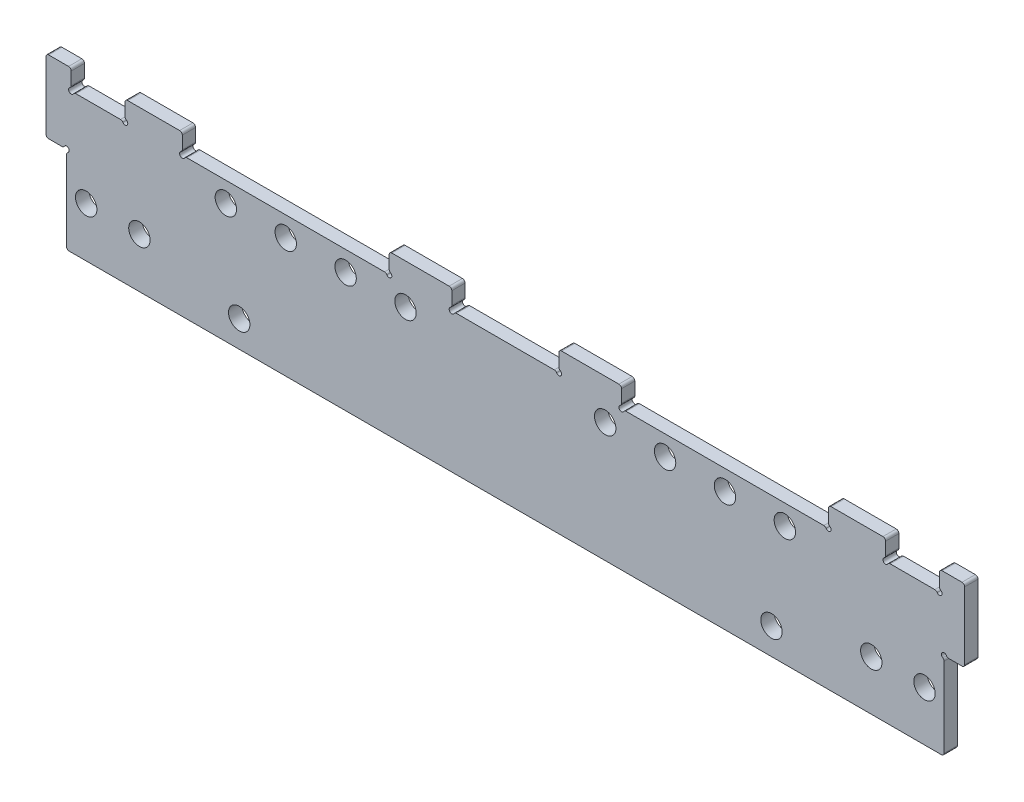
SolidWorks part; units mm, degrees
material "AISI Type A2 Tool Steel"
ref_plane "Front Plane" through (0, 0, 0) normal (0, 0, 1) x (1, 0, 0)
ref_plane "Top Plane" through (0, 0, 0) normal (0, 1, 0) x (1, 0, 0)
ref_plane "Right Plane" through (0, 0, 0) normal (1, 0, 0) x (0, 0, -1)
sketch "Top Layout" plane through (0, 0, 0) normal (0, 1, 0) x (1, 0, 0)
  line L0 (-114.046, -123.825) -> (-104.775, -123.825) construction
  line L1 (-104.775, -142.875) -> (-101.6, -142.875)
  line L2 (-104.775, -142.875) -> (-104.775, -104.775)
  line L3 (-104.775, -104.775) -> (-101.6, -104.775)
  line L4 (-101.6, -142.875) -> (-101.6, -104.775)
  line L5 (-104.775, -142.875) -> (-101.6, -104.775) construction
  line L6 (-104.775, -104.775) -> (-101.6, -142.875) construction
  line L7 (-19.05, -105.8164) -> (-101.6, -105.8164)
  line L8 (-19.05, -105.8164) -> (-19.05, -141.8336)
  line L9 (-19.05, -141.8336) -> (-101.6, -141.8336)
  line L10 (-101.6, -105.8164) -> (-101.6, -141.8336)
  line L11 (-19.05, -105.8164) -> (-101.6, -141.8336) construction
  line L12 (-19.05, -141.8336) -> (-101.6, -105.8164) construction
  line L13 (-133.096, -85.725) -> (-114.046, -85.725)
  line L14 (-133.096, -85.725) -> (-133.096, -161.925)
  line L15 (-133.096, -161.925) -> (-114.046, -161.925)
  line L16 (-114.046, -85.725) -> (-114.046, -161.925)
  line L17 (-133.096, -85.725) -> (-114.046, -161.925) construction
  line L18 (-133.096, -161.925) -> (-114.046, -85.725) construction
  line L19 (-104.775, -123.825) -> (0, -123.825) construction
  line L20 (0, -123.825) -> (0, 0) construction
  line L21 (-52.3528, -40.1717) -> (0, 0) construction
  line L22 (-70.6449, -16.3328) -> (-18.2922, 23.8388)
  line L23 (-34.0606, -64.0105) -> (18.2922, -23.8388)
  line L24 (-30.9251, 40.3023) -> (-122.2248, -29.7544)
  line L25 (-153.9748, -53.975) -> (-153.9748, -123.825)
  line L26 (-109.5248, -162.052) -> (109.5248, -162.052)
  line L27 (0, -162.052) -> (0, -123.825) construction
  line L28 (-109.5248, -162.052) -> (-109.5248, -20.0093) construction
  line L29 (-104.775, -142.875) -> (-104.775, -152.527)
  line L30 (-104.775, -152.527) -> (104.775, -152.527)
  line L31 (104.775, -104.775) -> (101.6, -104.775)
  line L32 (-144.4498, -73.025) -> (-109.5248, -73.025)
  line L33 (-144.4498, -73.025) -> (-144.4498, -123.825)
  line L34 (-144.4498, -123.825) -> (-109.5248, -123.825) construction
  line L35 (-109.5248, -73.025) -> (-109.5248, -162.052)
  line L36 (-144.4498, -73.025) -> (-109.5248, -123.825) construction
  line L37 (-144.4498, -123.825) -> (-109.5248, -73.025) construction
  line L38 (101.6, -142.875) -> (101.6, -104.775)
  line L39 (104.775, -142.875) -> (101.6, -142.875)
  line L40 (104.775, -142.875) -> (104.775, -104.775)
  line L41 (104.775, -142.875) -> (104.775, -152.527)
  line L42 (109.5248, -162.052) -> (109.5248, -20.0093) construction
  line L43 (30.9251, 40.3023) -> (122.2248, -29.7544)
  line L45 (19.05, -141.8336) -> (101.6, -141.8336)
  line L46 (101.6, -105.8164) -> (101.6, -141.8336)
  line L47 (19.05, -105.8164) -> (101.6, -105.8164)
  line L48 (19.05, -105.8164) -> (19.05, -141.8336)
  line L49 (133.096, -161.925) -> (114.046, -161.925)
  line L50 (114.046, -85.725) -> (114.046, -161.925)
  line L51 (133.096, -85.725) -> (114.046, -85.725)
  line L52 (133.096, -85.725) -> (133.096, -161.925)
  line L53 (144.4498, -123.825) -> (109.5248, -123.825) construction
  line L54 (109.5248, -73.025) -> (109.5248, -162.052)
  line L55 (144.4498, -73.025) -> (109.5248, -73.025)
  line L56 (144.4498, -73.025) -> (144.4498, -123.825)
  line L57 (-109.5248, -123.825) -> (-109.5248, -162.052) construction
  line L62 (-153.9748, -53.975) -> (-122.2248, -53.975)
  line L63 (-122.2248, -53.975) -> (-122.2248, -29.7544)
  line L64 (-144.4498, -123.825) -> (-153.9748, -123.825)
  line L65 (153.9748, -53.975) -> (153.9748, -123.825)
  line L66 (109.5248, -123.825) -> (109.5248, -162.052) construction
  line L67 (144.4498, -123.825) -> (153.9748, -123.825)
  line L68 (122.2248, -29.7544) -> (122.2248, -53.975)
  line L73 (-104.775, -104.775) -> (-104.775, -16.3647) construction
  line L74 (-95.25, -162.052) -> (-95.25, -9.0559) construction
  line L75 (-109.5248, -162.052) -> (-109.5248, -123.825) construction
  line L76 (109.5248, -162.052) -> (109.5248, -123.825) construction
  line L77 (122.2248, -53.975) -> (153.9748, -53.975)
  line L83 (104.775, -155.5496) -> (-104.775, -155.5496) construction
  line L88 (95.25, -162.052) -> (95.25, -9.0559) construction
  line L89 (104.775, -104.775) -> (104.775, -16.3647) construction
  line L92 (-104.775, -152.527) -> (-104.775, -162.052) construction
  line L93 (-14.605, -76.327) -> (14.605, -76.327)
  line L94 (-14.605, -76.327) -> (-14.605, -152.527)
  line L95 (-14.605, -152.527) -> (14.605, -152.527)
  line L96 (14.605, -76.327) -> (14.605, -152.527)
  line L97 (-14.605, -76.327) -> (14.605, -152.527) construction
  line L98 (-14.605, -152.527) -> (14.605, -76.327) construction
  line L99 (104.775, -152.527) -> (104.775, -162.052) construction
  line L100 (-19.05, -105.8164) -> (0, -105.8164) construction
  line L107 (0, -105.8164) -> (19.05, -105.8164) construction
  line L108 (104.775, -123.825) -> (114.046, -123.825) construction
  circle A0 centre (0, 0) radius 114.3
  circle A1 centre (0, 0) radius 6.35
  circle A2 centre (-52.3528, -40.1717) radius 17.8
  circle A3 centre (0, 0) radius 30.0482
  circle A4 centre (-52.3528, -40.1717) radius 30.0482
  arc A5 (-30.9251, 40.3023) -> (30.9251, 40.3023) centre (0, 0) cw
  point P2 (-103.1875, -123.825)
  point P7 (-60.325, -123.825)
  point P12 (-123.571, -123.825)
  point P30 (-126.9873, -98.425)
  point P35 (0, -114.427)
  point P53 (0, -152.527)
  dimension "D1" = 35.6
  dimension "D2" = 12.7
  dimension "D3" = 228.6
  dimension "D11" = 60.0964
  dimension "D12" = 50.8
  dimension "D14" = 52.5
  dimension "D4" = 3.175
  dimension "D5" = 19.05
  dimension "D6" = 76.2
  dimension "D7" = 82.55
  dimension "D8" = 38.1
  dimension "D9" = 104.775
  dimension "D10" = 18.0086
  dimension "D13" = 9.525
  dimension "D15" = 4.7498
  dimension "D16" = 9.525
  dimension "D17" = 9.652
  dimension "D18" = 50.8
  dimension "D19" = 12.446
  dimension "D20" = 65.9892
  dimension "D21" = 19.05
  dimension "D22" = 34.925
  dimension "D23" = 123.825
  dimension "D24" = 12.7
  dimension "D25" = 9.525
  dimension "D26" = 29.21
  dimension "D27" = 76.2
  dimension "D28" = 3.0226
sketch "Side Layout" plane through (0, 0, 0) normal (1, 0, 0) x (0, 0, -1)
  line L0 (0, -38.1) -> (0, 33.7344) construction
  line L1 (-114.3, -20.955) -> (114.3, -20.955)
  line L2 (-114.3, -20.955) -> (-114.3, -33.655)
  line L3 (-114.3, -33.655) -> (114.3, -33.655)
  line L4 (114.3, -20.955) -> (114.3, -33.655)
  line L5 (-114.3, -20.955) -> (114.3, -33.655) construction
  line L6 (-114.3, -33.655) -> (114.3, -20.955) construction
  line L7 (-9.525, -32.9406) -> (9.525, -32.9406)
  line L8 (-9.525, -32.9406) -> (-9.525, -38.1)
  line L9 (-9.525, -38.1) -> (9.525, -38.1)
  line L10 (9.525, -32.9406) -> (9.525, -38.1)
  line L11 (-9.525, -32.9406) -> (9.525, -38.1) construction
  line L12 (-9.525, -38.1) -> (9.525, -32.9406) construction
  line L13 (-11.9126, -29.3338) -> (11.9126, -29.3338)
  line L14 (-11.9126, -29.3338) -> (-11.9126, -32.9406)
  line L15 (-11.9126, -32.9406) -> (11.9126, -32.9406)
  line L16 (11.9126, -29.3338) -> (11.9126, -32.9406)
  line L17 (-11.9126, -29.3338) -> (11.9126, -32.9406) construction
  line L18 (-11.9126, -32.9406) -> (11.9126, -29.3338) construction
  line L19 (-6.35, -32.9406) -> (6.35, -32.9406)
  line L20 (-6.35, -32.9406) -> (-6.35, 33.7344)
  line L21 (-6.35, 33.7344) -> (6.35, 33.7344)
  line L22 (6.35, -32.9406) -> (6.35, 33.7344)
  line L23 (-6.35, -32.9406) -> (6.35, 33.7344) construction
  line L24 (-6.35, 33.7344) -> (6.35, -32.9406) construction
  line L25 (-162.052, 0) -> (-123.825, 0) construction
  line L26 (114.3, -33.655) -> (114.3, 0) construction
  line L27 (-142.875, 19.05) -> (-104.775, 19.05)
  line L28 (-40.1717, -9.525) -> (-40.1717, 5.4) construction
  line L29 (-142.875, 19.05) -> (-142.875, -19.05)
  line L30 (-142.875, -19.05) -> (-104.775, -19.05)
  line L31 (-104.775, 19.05) -> (-104.775, -19.05)
  line L32 (-142.875, 19.05) -> (-104.775, -19.05) construction
  line L33 (-142.875, -19.05) -> (-104.775, 19.05) construction
  line L34 (-130.175, -38.1) -> (-117.9516, -38.1) construction
  line L35 (-57.9717, -14.6) -> (-22.3717, -14.6)
  line L36 (-30.0482, -2.794) -> (30.0482, -2.794)
  line L37 (-30.0482, -2.794) -> (-30.0482, -20.955)
  line L38 (-30.0482, -20.955) -> (30.0482, -20.955)
  line L39 (30.0482, -2.794) -> (30.0482, -20.955)
  line L40 (-30.0482, -2.794) -> (30.0482, -20.955) construction
  line L41 (-30.0482, -20.955) -> (30.0482, -2.794) construction
  line L42 (-30.0482, -2.794) -> (-30.0482, 0) construction
  line L43 (-123.825, 0) -> (0, 0) construction
  line L44 (-57.9717, -14.6) -> (-57.9717, 25.4)
  line L45 (-57.9717, 25.4) -> (-22.3717, 25.4)
  line L46 (-22.3717, -14.6) -> (-22.3717, 25.4)
  line L47 (-19.05, 0) -> (19.05, 0)
  line L48 (-19.05, 0) -> (-19.05, -1.9812)
  line L49 (-19.05, -1.9812) -> (19.05, -1.9812)
  line L50 (19.05, 0) -> (19.05, -1.9812)
  line L51 (-19.05, 0) -> (19.05, -1.9812) construction
  line L52 (-19.05, -1.9812) -> (19.05, 0) construction
  line L53 (-70.2199, -3.175) -> (-10.1235, -3.175)
  line L54 (-70.2199, -3.175) -> (-70.2199, -15.875)
  line L55 (-70.2199, -15.875) -> (-10.1235, -15.875)
  line L56 (-10.1235, -3.175) -> (-10.1235, -15.875)
  line L57 (-70.2199, -3.175) -> (-10.1235, -15.875) construction
  line L58 (-70.2199, -15.875) -> (-10.1235, -3.175) construction
  line L59 (-40.1717, -9.525) -> (-40.1717, 0) construction
  line L60 (-57.9717, -14.6) -> (-22.3717, 25.4) construction
  line L61 (-57.9717, 25.4) -> (-22.3717, -14.6) construction
  line L62 (-22.3717, 0) -> (-57.9717, 0) construction
  line L63 (-137.8162, 0) -> (-123.825, -13.9912) construction
  line L64 (-139.065, 15.24) -> (-108.585, 15.24) construction
  line L65 (-139.065, 15.24) -> (-139.065, -15.24) construction
  line L66 (-139.065, -15.24) -> (-108.585, -15.24) construction
  line L67 (-108.585, 15.24) -> (-108.585, -15.24) construction
  line L68 (-139.065, 15.24) -> (-108.585, -15.24) construction
  line L69 (-139.065, -15.24) -> (-108.585, 15.24) construction
  line L70 (-137.8162, 0) -> (-123.825, 13.9912) construction
  line L71 (-123.825, -13.9912) -> (-109.8338, 0) construction
  line L72 (-123.825, 13.9912) -> (-109.8338, 0) construction
  line L73 (-137.8162, 0) -> (-109.8338, 0) construction
  line L74 (-123.825, -13.9912) -> (-123.825, 13.9912) construction
  line L75 (-6.35, 17.8594) -> (6.35, 17.8594)
  line L76 (114.3, 0) -> (-114.3, 0) construction
  line L77 (-22.3717, 19.05) -> (-6.35, 19.05) construction
  line L78 (-123.825, 38.1) -> (-97.9206, 38.1) construction
  line L79 (-19.05, -3.5814) -> (19.05, -3.5814)
  line L80 (-19.05, -3.5814) -> (-19.05, -1.9812)
  line L81 (-19.05, -1.9812) -> (19.05, -1.9812)
  line L82 (19.05, -3.5814) -> (19.05, -1.9812)
  line L83 (-19.05, -3.5814) -> (19.05, -1.9812) construction
  line L84 (-19.05, -1.9812) -> (19.05, -3.5814) construction
  line L85 (-8.7376, -16.7608) -> (8.7376, -16.7608)
  line L86 (-8.7376, -16.7608) -> (-8.7376, -29.3338)
  line L87 (-8.7376, -29.3338) -> (8.7376, -29.3338)
  line L88 (8.7376, -16.7608) -> (8.7376, -29.3338)
  line L89 (-8.7376, -16.7608) -> (8.7376, -29.3338) construction
  line L90 (-8.7376, -29.3338) -> (8.7376, -16.7608) construction
  line L91 (-8.7376, -3.5814) -> (8.7376, -3.5814)
  line L92 (-8.7376, -3.5814) -> (-8.7376, -16.1544)
  line L93 (-8.7376, -16.1544) -> (8.7376, -16.1544)
  line L94 (8.7376, -3.5814) -> (8.7376, -16.1544)
  line L95 (-8.7376, -3.5814) -> (8.7376, -16.1544) construction
  line L96 (-8.7376, -16.1544) -> (8.7376, -3.5814) construction
  circle A0 centre (-123.825, 0) radius 18.0086
  circle A1 centre (-123.825, 0) radius 38.1
  circle A2 centre (-139.065, 15.24) radius 1.905
  circle A3 centre (-108.585, 15.24) radius 1.905
  circle A4 centre (-108.585, -15.24) radius 1.905
  circle A5 centre (-139.065, -15.24) radius 1.905
  circle A6 centre (-137.8162, 0) radius 1.6002
  circle A7 centre (-123.825, 13.9912) radius 1.6002
  circle A8 centre (-109.8338, 0) radius 1.6002
  circle A9 centre (-123.825, -13.9912) radius 1.6002
  point P0 (0, -27.305)
  point P6 (0, -31.1372)
  point P7 (0, -35.5203)
  point P21 (0, 0.3969)
  point P32 (0, -11.8745)
  point P43 (0, -0.9906)
  point P55 (-40.1717, -9.525)
  point P72 (-40.1717, 5.4)
  point P88 (0, -23.0473)
  point P93 (0, -2.7813)
  point P102 (0, -9.8679)
  dimension "D17" = 3.81
  dimension "D18" = 3.2004
  dimension "D1" = 12.7
  dimension "D2" = 5.1594
  dimension "D3" = 19.05
  dimension "D4" = 3.6068
  dimension "D5" = 23.8252
  dimension "D6" = 12.7
  dimension "D7" = 18.161
  dimension "D8" = 1.9812
  dimension "D9" = 12.7
  dimension "D10" = 40
  dimension "D11" = 25.4
  dimension "D12" = 50.8
  dimension "D13" = 41.275
  dimension "D14" = 30.48
  dimension "D15" = 4.445
  dimension "D16" = 19.7866
  dimension "D19" = 15.875
  dimension "D20" = 6.35
  dimension "D21" = 38.1
  dimension "D22" = 1.6002
  dimension "D23" = 38.1
  dimension "D24" = 17.4752
  dimension "D25" = 12.573
ref_plane "Plane1" through (0, 25.4, 0) normal (0, 1, 0) x (1, 0, 0)
sketch "Sketch3" plane through (0, 25.4, 0) normal (0, 1, 0) x (1, 0, 0)
  line L0 (-104.775, -36.3747) -> (-30.9251, 20.2924)
  line L1 (-104.775, -104.775) -> (-104.775, -16.3647) construction
  line L2 (0, -200130.175) -> (0, 199882.0484) construction
  line L3 (-30.9251, 40.3023) -> (-122.2248, -29.7544) construction
  line L5 (-104.775, -36.3747) -> (-104.775, -77.6497)
  line L6 (-92.075, -77.6497) -> (-104.775, -77.6497)
  line L7 (30.9251, 20.2924) -> (104.775, -36.3747)
  line L8 (104.775, -77.6497) -> (92.075, -77.6497)
  line L9 (104.775, -36.3747) -> (104.775, -77.6497)
  line L11 (104.775, -104.775) -> (104.775, -16.3647) construction
  line L12 (30.9251, 40.3023) -> (122.2248, -29.7544) construction
  line L13 (92.075, -74.6536) -> (24.1423, -22.5271)
  line L14 (-32.2514, -66.3682) -> (20.1013, -26.1965)
  line L15 (-30.9251, 20.2924) -> (0, 44.022)
  line L16 (0, 44.022) -> (30.9251, 20.2924)
  line L17 (-92.075, -77.6497) -> (-92.075, -73.1917)
  line L19 (-92.075, -73.1917) -> (-52.3528, -73.1917)
  line L20 (92.075, -74.6536) -> (92.075, -77.6497)
  circle A0 centre (-52.3528, -40.1717) radius 17.8 construction
  circle A1 centre (-52.3528, -40.1717) radius 17.8
  circle A2 centre (0, 0) radius 6.35
  circle A3 centre (0, 0) radius 6.35 construction
  arc A4 (-52.3528, -73.1917) -> (-32.2514, -66.3682) centre (-52.3528, -40.1717) ccw
  arc A5 (20.1013, -26.1965) -> (24.1423, -22.5271) centre (0, 0) ccw
  arc A6 (30.9251, 20.2924) -> (-30.9251, 20.2924) centre (0, -20.01) ccw construction
  point P28 (0, 44.022)
  dimension "D1" = 33.02
  dimension "D5" = 50.8
  dimension "D2" = 41.275
  dimension "D3" = 34.925
  dimension "D4" = 12.7
  dimension "D6" = 38.1
ref_plane "Plane3" through (-104.775, 0, 0) normal (-1, 0, 0) x (0, 0, 1)
sketch "Sketch6" plane through (-104.775, 0, 0) normal (-1, 0, 0) x (0, 0, 1)
  line L0 (162.052, -25.4) -> (162.052, 25.4)
  line L1 (162.052, 25.4) -> (77.6497, 25.4)
  line L2 (36.3747, 25.4) -> (77.6497, 25.4) construction
  line L3 (147.7645, 11.1125) -> (162.052, 11.1125) construction
  line L4 (162.052, 0) -> (71.2997, 0) construction
  line L5 (77.6497, 25.4) -> (77.6497, 19.05)
  line L6 (77.6497, 19.05) -> (36.3747, 19.05)
  line L7 (36.3747, 19.05) -> (36.3747, 6.35)
  line L8 (36.3747, 6.35) -> (71.2997, 6.35)
  line L10 (99.6315, -3.175) -> (99.6315, 11.1125) construction
  line L11 (71.2997, -25.4) -> (162.052, -25.4)
  line L13 (71.2997, 6.35) -> (71.2997, -25.4)
  line L14 (152.527, -25.4) -> (152.527, 25.4) construction
  line L15 (99.6315, 11.1125) -> (99.6315, 25.4) construction
  line L16 (147.7645, 11.1125) -> (147.7645, 25.4) construction
  line L17 (94.869, -7.9375) -> (104.394, -7.9375) construction
  line L18 (94.869, -7.9375) -> (94.869, 25.4) construction
  line L19 (94.869, 25.4) -> (104.394, 25.4) construction
  line L20 (104.394, -7.9375) -> (104.394, 25.4) construction
  line L21 (94.869, -7.9375) -> (104.394, 25.4) construction
  line L22 (94.869, 25.4) -> (104.394, -7.9375) construction
  line L23 (147.7645, 11.1125) -> (147.7645, -3.175) construction
  line L24 (104.394, -7.9375) -> (123.825, -7.9375) construction
  line L25 (143.002, -7.9375) -> (152.527, -7.9375) construction
  line L26 (143.002, -7.9375) -> (143.002, 25.4) construction
  line L27 (143.002, 25.4) -> (152.527, 25.4) construction
  line L28 (152.527, -7.9375) -> (152.527, 25.4) construction
  line L29 (143.002, -7.9375) -> (152.527, 25.4) construction
  line L30 (143.002, 25.4) -> (152.527, -7.9375) construction
  line L31 (123.825, -7.9375) -> (152.527, -7.9375) construction
  line L32 (104.775, 19.05) -> (104.775, -19.05) construction
  line L34 (155.702, -25.4) -> (155.702, 25.4) construction
  circle A0 centre (109.8338, 0) radius 1.6002 construction
  circle A1 centre (123.825, 13.9912) radius 1.6002 construction
  circle A2 centre (137.8162, 0) radius 1.6002 construction
  circle A3 centre (123.825, -13.9912) radius 1.6002 construction
  circle A4 centre (109.8338, 0) radius 1.6002 construction
  circle A5 centre (123.825, 13.9912) radius 1.6002 construction
  circle A6 centre (137.8162, 0) radius 1.6002 construction
  circle A7 centre (123.825, -13.9912) radius 1.6002 construction
  circle A8 centre (123.825, 0) radius 18.0086 construction
  circle A9 centre (123.825, 0) radius 18.0086 construction
  circle A10 centre (123.825, 0) radius 9.525
  circle A11 centre (108.585, -15.24) radius 1.905 construction
  circle A12 centre (108.585, 15.24) radius 1.905 construction
  circle A13 centre (139.065, 15.24) radius 1.905 construction
  circle A14 centre (139.065, -15.24) radius 1.905 construction
  circle A15 centre (108.585, -15.24) radius 1.905
  circle A16 centre (108.585, 15.24) radius 1.905
  circle A17 centre (139.065, 15.24) radius 1.905
  circle A18 centre (139.065, -15.24) radius 1.905
  circle A19 centre (147.7645, 11.1125) radius 2.5527
  circle A26 centre (99.6315, 11.1125) radius 2.5527
  circle A27 centre (99.6315, -3.175) radius 2.5527
  circle A28 centre (147.7645, -3.175) radius 2.5527
  point P29 (0, 0)
  point P55 (99.6315, 8.7312)
  point P61 (147.7645, 8.7312)
  dimension "D4" = 19.05
  dimension "D7" = 5.1054
  dimension "D1" = 6.35
  dimension "D2" = 12.7
  dimension "D3" = 25.4
  dimension "D5" = 6.35
  dimension "D6" = 3.175
  dimension "D8" = 0.381
  dimension "D9" = 14.2875
  dimension "D10" = 9.525
  dimension "D12" = 33.3375
ref_plane "Plane4" through (0, 19.05, 0) normal (0, 1, 0) x (1, 0, 0)
sketch "Sketch12" plane through (0, 19.05, 0) normal (0, 1, 0) x (1, 0, 0)
  line L0 (-104.775, -77.6497) -> (-104.775, -36.3747)
  line L1 (-104.775, -36.3747) -> (-92.075, -36.3747)
  line L3 (-92.075, -36.3747) -> (-92.075, -77.6497)
  line L5 (-92.075, -77.6497) -> (-104.775, -77.6497)
  line L6 (-98.425, -77.6497) -> (-98.425, -63.3622) construction
  line L7 (-98.425, -63.3622) -> (-98.425, -50.6622) construction
  line L8 (-98.425, -50.6622) -> (-98.425, -36.3747) construction
  line L10 (-98.425, -36.3747) -> (-104.775, -36.3747) construction
  circle A0 centre (-98.425, -63.3622) radius 2.5527
  circle A1 centre (-98.425, -50.6622) radius 2.5527
  dimension "D2" = 5.1054
  dimension "D1" = 12.7
  dimension "D3" = 12.7
ref_plane "Plane5" through (0, 0, 152.527) normal (0, 0, 1) x (1, 0, 0)
sketch "Sketch41" plane through (0, 0, 152.527) normal (0, 0, 1) x (1, 0, 0)
  line L0 (-104.775, -7.9375) -> (-104.775, 25.4) construction
  line L1 (-104.775, -7.9375) -> (-104.775, 12.7)
  line L2 (-104.775, -7.9375) -> (104.775, -7.9375)
  line L3 (104.775, -7.9375) -> (104.775, 12.7)
  line L4 (104.775, 25.4) -> (-104.775, 25.4)
  line L5 (0, -7.9375) -> (0, 25.4) construction
  line L6 (-104.775, 3.9624) -> (-100.0125, 3.9624) construction
  line L7 (-100.0125, 3.9624) -> (-100.0125, 25.4) construction
  line L8 (104.775, 3.9624) -> (100.0125, 3.9624) construction
  line L9 (100.0125, 3.9624) -> (100.0125, 25.4) construction
  line L10 (19.05, 20.6375) -> (23.8252, 20.6375) construction
  line L11 (19.05, 15.875) -> (78.5876, 15.875) construction
  line L12 (19.05, 15.875) -> (19.05, 25.4) construction
  line L13 (19.05, 25.4) -> (78.5876, 25.4) construction
  line L14 (78.5876, 15.875) -> (78.5876, 25.4) construction
  line L15 (19.05, 15.875) -> (78.5876, 25.4) construction
  line L16 (19.05, 25.4) -> (78.5876, 15.875) construction
  line L17 (23.8252, 20.6375) -> (38.1127, 20.6375) construction
  line L18 (38.1127, 20.6375) -> (52.4002, 20.6375) construction
  line L19 (52.4002, 20.6375) -> (66.6877, 20.6375) construction
  line L20 (-104.775, 25.4) -> (-112.395, 25.4)
  line L21 (-112.395, 25.4) -> (-112.395, 3.175)
  line L22 (-112.395, 3.175) -> (-109.5248, 3.175)
  line L23 (-109.5248, 3.175) -> (-109.5248, 12.7)
  line L24 (-109.5248, 12.7) -> (-104.775, 12.7)
  line L25 (-104.775, 12.7) -> (-104.775, 25.4) construction
  line L26 (104.775, 25.4) -> (112.395, 25.4)
  line L27 (112.395, 25.4) -> (112.395, 3.175)
  line L28 (112.395, 3.175) -> (109.5248, 3.175)
  line L29 (109.5248, 3.175) -> (109.5248, 12.7)
  line L30 (109.5248, 12.7) -> (104.775, 12.7)
  line L31 (104.775, 12.7) -> (104.775, 25.4) construction
  line L32 (-100.0125, 3.9624) -> (-87.3125, 3.9624) construction
  line L33 (-63.5, -1.5875) -> (0, -1.5875) construction
  line L34 (0, -1.5875) -> (63.5, -1.5875) construction
  line L35 (63.5, -1.5875) -> (63.5, -7.9375) construction
  circle A0 centre (-100.0125, 3.9624) radius 2.5527
  circle A1 centre (100.0125, 3.9624) radius 2.5527
  circle A2 centre (23.8252, 20.6375) radius 2.5527
  circle A3 centre (38.1127, 20.6375) radius 2.5527
  circle A4 centre (52.4002, 20.6375) radius 2.5527
  circle A5 centre (66.6877, 20.6375) radius 2.5527
  circle A6 centre (-66.6877, 20.6375) radius 2.5527
  circle A7 centre (-52.4002, 20.6375) radius 2.5527
  circle A8 centre (-38.1127, 20.6375) radius 2.5527
  circle A9 centre (-23.8252, 20.6375) radius 2.5527
  circle A10 centre (-87.3125, 3.9624) radius 2.5527
  circle A11 centre (87.3125, 3.9624) radius 2.5527
  circle A12 centre (-63.5, -1.5875) radius 2.5527
  circle A13 centre (63.5, -1.5875) radius 2.5527
  point P14 (48.8188, 20.6375)
  dimension "D3" = 5.1054
  dimension "D7" = 5.1054
  dimension "D1" = 21.4376
  dimension "D2" = 4.7625
  dimension "D4" = 9.525
  dimension "D5" = 59.5376
  dimension "D6" = 4.7752
  dimension "D8" = 14.2875
  dimension "D9" = 7.62
  dimension "D10" = 4.7498
  dimension "D11" = 12.7
  dimension "D12" = 9.525
  dimension "D13" = 19.05
  dimension "D14" = 12.7
  dimension "D15" = 6.35
  dimension "D16" = 63.5
extrude "Back Plate Extrude------------" add sketch "Sketch41" along normal blind 3.175
sketch "Sketch44" plane through (0, 25.4, 0) normal (0, 1, 0) x (1, 0, 0)
  line L0 (73.8315, -147.7645) -> (73.8315, -152.527) construction
  line L1 (92.075, -74.6536) -> (92.075, -77.6497) construction
  line L2 (-92.075, -77.6497) -> (-92.075, -73.1917) construction
  line L3 (0, -123.825) -> (0, 0) construction
  line L4 (-92.075, -73.1917) -> (-52.3528, -73.1917) construction
  line L5 (-104.775, -104.775) -> (-104.775, -16.3647) construction
  line L6 (-32.2514, -66.3682) -> (20.1013, -26.1965) construction
  line L21 (-104.775, -68.1247) -> (-104.775, -152.527)
  line L22 (-104.775, -152.527) -> (104.775, -152.527)
  line L23 (104.775, -152.527) -> (104.775, -68.1247)
  line L34 (-104.775, -99.6315) -> (-100.0125, -99.6315) construction
  line L35 (-104.775, -147.7645) -> (-100.0125, -147.7645) construction
  line L36 (0, -152.527) -> (0, -35.6178) construction
  line L38 (30.969, -147.7645) -> (45.2565, -147.7645) construction
  line L39 (45.2565, -147.7645) -> (59.544, -147.7645) construction
  line L40 (59.544, -147.7645) -> (73.8315, -147.7645) construction
  line L41 (23.8252, -152.527) -> (30.969, -152.527) construction
  line L42 (104.775, -152.527) -> (-104.775, -152.527) construction
  line L43 (30.969, -152.527) -> (38.1127, -152.527) construction
  line L44 (30.969, -152.527) -> (30.969, -147.7645) construction
  line L45 (-92.075, -77.6497) -> (-104.775, -77.6497) construction
  line L48 (-35.1507, -62.5899) -> (-8.9743, -42.504) construction
  line L49 (-8.9743, -42.504) -> (17.2021, -22.4182) construction
  line L50 (45.5313, -32.9364) -> (87.3125, -64.9962) construction
  line L51 (92.075, -74.6536) -> (24.1423, -22.5271) construction
  line L52 (104.775, -77.6497) -> (92.075, -77.6497) construction
  line L79 (-104.775, -68.1247) -> (-92.075, -68.1247)
  line L80 (-92.075, -68.1247) -> (-92.075, -63.6667)
  line L85 (21.8118, -8.7328) -> (92.075, -62.6476)
  line L86 (-38.0499, -58.8115) -> (14.3028, -18.6398)
  line L87 (-92.075, -63.6667) -> (-52.3528, -63.6667)
  line L88 (92.075, -62.6476) -> (92.075, -68.1247)
  line L89 (92.075, -68.1247) -> (104.775, -68.1247)
  circle A0 centre (-73.8315, -147.7645) radius 2.5527
  circle A1 centre (-59.544, -147.7645) radius 2.5527
  circle A2 centre (-45.2565, -147.7645) radius 2.5527
  circle A3 centre (-30.969, -147.7645) radius 2.5527
  circle A17 centre (-100.0125, -99.6315) radius 2.5527
  circle A18 centre (-100.0125, -147.7645) radius 2.5527
  circle A19 centre (100.0125, -147.7645) radius 2.5527
  circle A20 centre (100.0125, -99.6315) radius 2.5527
  circle A21 centre (30.969, -147.7645) radius 2.5527
  circle A22 centre (45.2565, -147.7645) radius 2.5527
  circle A23 centre (59.544, -147.7645) radius 2.5527
  circle A24 centre (73.8315, -147.7645) radius 2.5527
  circle A25 centre (-87.3125, -68.4292) radius 4.7625 construction
  circle A26 centre (-35.1507, -62.5899) radius 4.7625 construction
  circle A27 centre (-8.9743, -42.504) radius 4.7625 construction
  circle A28 centre (17.2021, -22.4182) radius 4.7625 construction
  circle A29 centre (45.5313, -32.9364) radius 4.7625 construction
  circle A30 centre (87.3125, -64.9962) radius 4.7625 construction
  circle A32 centre (-87.3125, -68.4292) radius 2.5527
  circle A33 centre (-35.1507, -62.5899) radius 2.5527
  circle A34 centre (-8.9743, -42.504) radius 2.5527 construction
  circle A35 centre (17.2021, -22.4182) radius 2.5527
  circle A36 centre (45.5313, -32.9364) radius 2.5527
  circle A37 centre (87.3125, -64.9962) radius 2.5527
  circle A38 centre (-97.155, -85.2697) radius 7.62 construction
  circle A39 centre (97.155, -85.2697) radius 7.62 construction
  circle A40 centre (24.5121, -32.4156) radius 7.62 construction
  arc A41 (20.1013, -26.1965) -> (24.1423, -22.5271) centre (0, 0) ccw construction
  circle A42 centre (-97.155, -85.2697) radius 2.5527
  circle A43 centre (24.5121, -32.4156) radius 2.5527
  circle A44 centre (97.155, -85.2697) radius 2.5527
  arc A56 (14.3028, -18.6398) -> (21.8118, -8.7328) centre (0, 0) ccw
  arc A57 (-52.3528, -63.6667) -> (-38.0499, -58.8115) centre (-52.3528, -40.1717) ccw
  point P4 (-104.775, -152.527)
  dimension "D2" = 5.1054
  dimension "D7" = 5.1054
  dimension "D8" = 15.24
  dimension "D3" = 9.525
  dimension "D9" = 9.525
  dimension "D4" = 4.7625
  dimension "D5" = 14.2875
  dimension "D6" = 9.525
  dimension "D1" = 4.7625
  dimension "D10" = 52.664
sketch "Sketch72" plane through (0, 25.4, 0) normal (0, 1, 0) x (1, 0, 0)
  line L0 (-104.775, -68.1247) -> (-104.775, -152.527) construction
  line L1 (-104.775, -152.527) -> (-109.5248, -152.527)
  line L2 (-104.775, -152.527) -> (-104.775, -135.0645)
  line L3 (-104.775, -135.0645) -> (-109.5248, -135.0645)
  line L4 (-109.5248, -152.527) -> (-109.5248, -135.0645)
  line L5 (-104.775, -152.527) -> (-109.5248, -135.0645) construction
  line L6 (-104.775, -135.0645) -> (-109.5248, -152.527) construction
  line L7 (-104.775, -152.527) -> (104.775, -152.527) construction
  line L8 (-77.0065, -152.527) -> (-73.8315, -147.7645) construction
  line L9 (-77.0065, -152.527) -> (-27.794, -152.527)
  line L10 (-77.0065, -152.527) -> (-77.0065, -155.5496)
  line L11 (-77.0065, -155.5496) -> (-27.794, -155.5496)
  line L12 (-27.794, -152.527) -> (-27.794, -155.5496)
  line L13 (-77.0065, -152.527) -> (-27.794, -155.5496) construction
  line L14 (-77.0065, -155.5496) -> (-27.794, -152.527) construction
  line L15 (-27.794, -152.527) -> (-30.969, -147.7645) construction
  line L16 (-77.0065, -152.527) -> (-77.0065, -147.7645) construction
  line L18 (-104.775, -93.5247) -> (-109.5248, -93.5247)
  line L19 (-104.775, -93.5247) -> (-104.775, -112.3315)
  line L20 (-104.775, -112.3315) -> (-109.5248, -112.3315)
  line L21 (-109.5248, -93.5247) -> (-109.5248, -112.3315)
  line L22 (-104.775, -93.5247) -> (-109.5248, -112.3315) construction
  line L23 (-104.775, -112.3315) -> (-109.5248, -93.5247) construction
  line L24 (0, -152.527) -> (-12.7, -152.527)
  line L25 (0, -152.527) -> (0, -155.5496)
  line L26 (0, -155.5496) -> (-12.7, -155.5496)
  line L27 (-12.7, -152.527) -> (-12.7, -155.5496)
  line L28 (0, -152.527) -> (-12.7, -155.5496) construction
  line L29 (0, -155.5496) -> (-12.7, -152.527) construction
  line L30 (-104.775, -68.1247) -> (-109.5248, -68.1247)
  line L31 (-104.775, -68.1247) -> (-104.775, -77.6497)
  line L32 (-104.775, -77.6497) -> (-109.5248, -77.6497)
  line L33 (-109.5248, -68.1247) -> (-109.5248, -77.6497)
  line L34 (-104.775, -68.1247) -> (-109.5248, -77.6497) construction
  line L35 (-104.775, -77.6497) -> (-109.5248, -68.1247) construction
  line L38 (-103.505, -155.5496) -> (-90.805, -155.5496)
  line L39 (-90.805, -152.527) -> (-90.805, -155.5496)
  line L40 (-103.505, -155.5496) -> (-103.505, -152.527)
  line L41 (-103.505, -155.5496) -> (-90.805, -152.527) construction
  line L42 (-103.505, -152.527) -> (-90.805, -152.527)
  line L43 (-77.0065, -147.7645) -> (-73.8315, -147.7645) construction
  line L44 (-103.505, -152.527) -> (-101.5221, -149.823) construction
  circle A0 centre (-100.0125, -147.7645) radius 2.5527 construction
  circle A1 centre (-73.8315, -147.7645) radius 2.5527 construction
  circle A2 centre (-30.969, -147.7645) radius 2.5527 construction
  point P4 (-107.1499, -143.7958)
  point P5 (-100.0125, -147.7645)
  point P16 (-52.4002, -154.0383)
  point P18 (-97.155, -154.0383)
  point P25 (-107.1499, -102.9281)
  point P34 (-6.35, -154.0383)
  point P39 (-107.1499, -72.8872)
  dimension "D1" = 4.7498
  dimension "D2" = 12.7
  dimension "D3" = 12.7
  dimension "D4" = 12.7
  dimension "D5" = 9.525
  dimension "D6" = 15.875
  dimension "D7" = 12.7
  dimension "D8" = 3.175
  dimension "D9" = 1.27
  dimension "D10" = 3.0226
sketch "Sketch71" plane through (0, 0, 155.702) normal (0, 0, 1) x (1, 0, 0)
  line L1 (-112.395, 25.4) -> (-103.505, 25.4)
  line L2 (-112.395, 25.4) -> (-112.395, 30.1625)
  line L3 (-112.395, 30.1625) -> (-103.505, 30.1625)
  line L4 (-103.505, 25.4) -> (-103.505, 30.1625)
  line L5 (-112.395, 25.4) -> (-103.505, 30.1625) construction
  line L6 (-112.395, 30.1625) -> (-103.505, 25.4) construction
  line L13 (112.395, 25.4) -> (-112.395, 25.4) construction
  line L15 (-90.805, 25.4) -> (-77.0065, 25.4)
  line L16 (-90.805, 25.4) -> (-90.805, 30.1625)
  line L17 (-90.805, 30.1625) -> (-77.0065, 30.1625)
  line L18 (-77.0065, 25.4) -> (-77.0065, 30.1625)
  line L19 (-90.805, 25.4) -> (-77.0065, 30.1625) construction
  line L20 (-90.805, 30.1625) -> (-77.0065, 25.4) construction
  line L21 (-27.794, 25.4) -> (-12.7, 25.4)
  line L22 (-27.794, 25.4) -> (-27.794, 30.1625)
  line L23 (-27.794, 30.1625) -> (-12.7, 30.1625)
  line L24 (-12.7, 25.4) -> (-12.7, 30.1625)
  line L25 (-27.794, 25.4) -> (-12.7, 30.1625) construction
  line L26 (-27.794, 30.1625) -> (-12.7, 25.4) construction
  point P4 (-107.95, 27.7812)
  point P20 (-83.9057, 27.7812)
  point P25 (-20.247, 27.7812)
  dimension "D1" = 4.7625
extrude "Boss-Extrude26" add sketch "Sketch71" against normal through all
mirror "Mirror23" about plane through (0, 0, 0) normal (1, 0, 0) of "Boss-Extrude26"
sketch "Sketch91" plane through (0, 0, 152.527) normal (0, 0, -1) x (-1, 0, 0)
  line L1 (-109.601, -7.9375) -> (-104.6988, -7.9375)
  line L2 (-109.601, -7.9375) -> (-109.601, 12.827)
  line L3 (-109.601, 12.827) -> (-104.6988, 12.827)
  line L4 (-104.6988, -7.9375) -> (-104.6988, 12.827)
  line L5 (-109.601, -7.9375) -> (-104.6988, 12.827) construction
  line L6 (-109.601, 12.827) -> (-104.6988, -7.9375) construction
  line L8 (-109.5248, 12.7) -> (-109.5248, 3.175) construction
  line L9 (104.775, -7.9375) -> (-104.775, -7.9375) construction
  line L10 (-103.505, 30.1625) -> (-112.395, 30.1625) construction
  line L11 (-103.5812, 30.1625) -> (-90.7288, 30.1625)
  line L12 (-103.5812, 30.1625) -> (-103.5812, 25.4)
  line L13 (-103.5812, 25.4) -> (-90.7288, 25.4)
  line L14 (-90.7288, 30.1625) -> (-90.7288, 25.4)
  line L15 (-103.5812, 30.1625) -> (-90.7288, 25.4) construction
  line L16 (-103.5812, 25.4) -> (-90.7288, 30.1625) construction
  line L17 (-103.505, 25.4) -> (-90.805, 25.4) construction
  line L18 (-103.505, 25.4) -> (-103.505, 30.1625) construction
  line L19 (-77.0065, 30.1625) -> (-90.805, 30.1625) construction
  line L20 (-77.0827, 30.1625) -> (-27.7178, 30.1625)
  line L21 (-77.0827, 30.1625) -> (-77.0827, 25.4)
  line L22 (-77.0827, 25.4) -> (-27.7178, 25.4)
  line L23 (-27.7178, 30.1625) -> (-27.7178, 25.4)
  line L24 (-77.0827, 30.1625) -> (-27.7178, 25.4) construction
  line L25 (-77.0827, 25.4) -> (-27.7178, 30.1625) construction
  line L26 (-77.0065, 25.4) -> (-27.794, 25.4) construction
  line L27 (-77.0065, 25.4) -> (-77.0065, 30.1625) construction
  line L28 (-12.7, 25.4) -> (12.7, 25.4) construction
  line L29 (0, 25.4) -> (-12.7762, 25.4)
  line L30 (0, 25.4) -> (0, 30.1625)
  line L31 (0, 30.1625) -> (-12.7762, 30.1625)
  line L32 (-12.7762, 25.4) -> (-12.7762, 30.1625)
  line L33 (0, 25.4) -> (-12.7762, 30.1625) construction
  line L34 (0, 30.1625) -> (-12.7762, 25.4) construction
  line L35 (-12.7, 30.1625) -> (-27.794, 30.1625) construction
  line L36 (-12.7, 25.4) -> (-12.7, 30.1625) construction
  line L37 (-107.1499, 12.7) -> (-107.1499, 12.827) construction
  line L38 (-104.775, 12.7) -> (-109.5248, 12.7) construction
  point P4 (-107.1499, 2.4447)
  point P18 (-97.155, 27.7812)
  point P22 (-97.155, 25.4)
  point P23 (-97.155, 25.4)
  point P30 (-52.4002, 27.7812)
  point P35 (-52.4002, 25.4)
  point P36 (-52.4002, 25.4)
  point P43 (-6.3881, 27.7812)
  dimension "D1" = 0.0762
  dimension "D2" = 0.0762
  dimension "D3" = 0.0762
  dimension "D4" = 0.0762
  dimension "D5" = 0.127
extrude "Back Plate Tolerences" cut sketch "Sketch91" against normal through all
mirror "Mirror25" about plane through (0, 0, 0) normal (1, 0, 0) of "Back Plate Tolerences"
sketch "Sketch92" plane through (0, 0, 155.702) normal (0, 0, 1) x (1, 0, 0)
  line L1 (-112.395, 30.1625) -> (-109.601, 30.1625)
  line L2 (-112.395, 30.1625) -> (-112.395, 3.175)
  line L3 (-112.395, 3.175) -> (-109.601, 3.175)
  line L4 (-109.601, 30.1625) -> (-109.601, 3.175)
  line L5 (-112.395, 30.1625) -> (-109.601, 3.175) construction
  line L6 (-112.395, 3.175) -> (-109.601, 30.1625) construction
  line L7 (112.395, 30.1625) -> (109.601, 30.1625)
  line L8 (112.395, 30.1625) -> (112.395, 3.175)
  line L9 (112.395, 3.175) -> (109.601, 3.175)
  line L10 (109.601, 30.1625) -> (109.601, 3.175)
  line L11 (112.395, 30.1625) -> (109.601, 3.175) construction
  line L12 (112.395, 3.175) -> (109.601, 30.1625) construction
  point P4 (-110.998, 16.6687)
  point P11 (110.998, 16.6687)
extrude "Cut-Extrude1" cut sketch "Sketch92" against normal through all
fillet "Fillet27" radius 0.635 6 edges at (-104.6988, -7.9375, 154.1145) (104.6988, -7.9375, 154.1145) (109.601, 12.827, 154.1145) (109.601, 30.1625, 154.1145) (-109.601, 12.827, 154.1145) (-109.601, 30.1625, 154.1145)
fillet "Fillet28" radius 0.635 10 edges at (103.5812, 30.1625, 154.1145) (90.7288, 30.1625, 154.1145) (77.0827, 30.1625, 154.1145) (27.7178, 30.1625, 154.1145) (12.7762, 30.1625, 154.1145) (-12.7762, 30.1625, 154.1145) (-27.7178, 30.1625, 154.1145) (-77.0827, 30.1625, 154.1145) (-90.7288, 30.1625, 154.1145) (-103.5812, 30.1625, 154.1145)
sketch "Sketch93" plane through (0, 0, 155.702) normal (0, 0, 1) x (1, 0, 0)
  circle A0 centre (-104.6988, 12.827) radius 0.635
  circle A1 centre (-103.5812, 25.4) radius 0.635
  circle A2 centre (-90.7288, 25.4) radius 0.635
  circle A3 centre (-77.0827, 25.4) radius 0.635
  circle A4 centre (-27.7178, 25.4) radius 0.635
  circle A5 centre (-12.7762, 25.4) radius 0.635
  dimension "D1" = 1.27
extrude "Cut-Extrude2" cut sketch "Sketch93" against normal through all
fillet "Fillet29" radius 0.635 12 edges at (-12.1412, 25.4, 154.1145) (-12.7762, 26.035, 154.1145) (-27.7178, 26.035, 154.1145) (-28.3528, 25.4, 154.1145) (-76.4477, 25.4, 154.1145) (-77.0827, 26.035, 154.1145) (-90.7288, 26.035, 154.1145) (-91.3638, 25.4, 154.1145) (-103.5812, 26.035, 154.1145) (-102.9462, 25.4, 154.1145) (-105.3338, 12.827, 154.1145) (-104.6988, 12.192, 154.1145)
mirror "Mirror26" about plane through (0, 0, 0) normal (1, 0, 0) of "Cut-Extrude2", "Fillet29"
